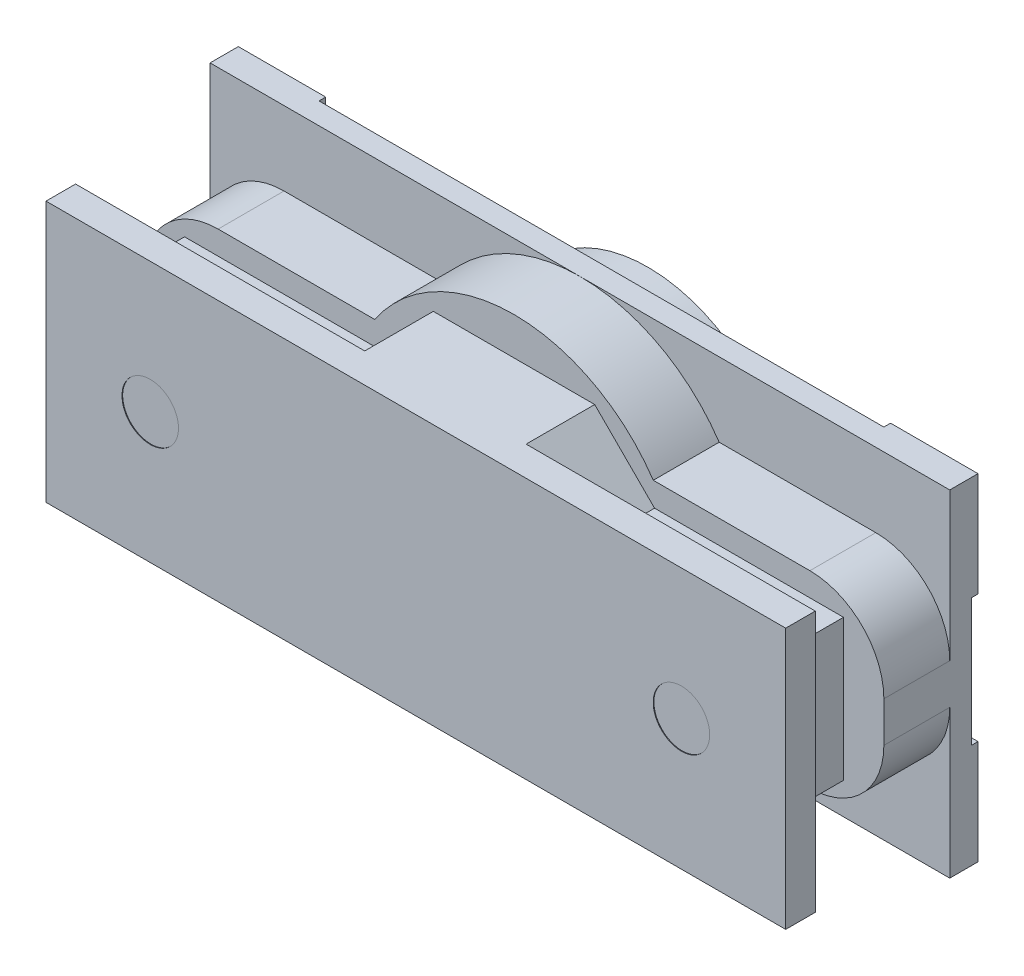
SolidWorks part; units mm, degrees
ref_plane "Płaszczyzna przednia" through (0, 0, 0) normal (0, 0, 1) x (1, 0, 0)
ref_plane "Płaszczyzna górna" through (0, 0, 0) normal (0, 1, 0) x (1, 0, 0)
ref_plane "Płaszczyzna prawa" through (0, 0, 0) normal (1, 0, 0) x (0, 0, -1)
sketch "Szkic1" plane through (0, 0, 0) normal (0, 0, 1) x (1, 0, 0)
  line L1 (-55, -25) -> (55, -25)
  line L2 (-55, -25) -> (-55, 25)
  line L3 (-55, 25) -> (55, 25)
  line L4 (55, -25) -> (55, 25)
  line L5 (-55, -25) -> (55, 25) construction
  line L6 (-55, 25) -> (55, -25) construction
  point P0 (0, 0)
  dimension "D1" = 110
  dimension "D2" = 50
extrude "Dodanie-wyciągnięcie1" add sketch "Szkic1" along normal blind 4.2
sketch "Szkic2" plane through (0, 0, 0) normal (0, 0, 1) x (1, 0, 0)
  circle A0 centre (0, 0) radius 21.15
  dimension "D1" = 42.3
extrude "Dodanie-wyciągnięcie2" add sketch "Szkic2" against normal blind 5.9
sketch "Szkic3" plane through (0, 0, 4.2) normal (0, 0, 1) x (1, 0, 0)
  line L0 (55, -25) -> (55, 25) construction
  line L1 (-55, -14) -> (55, -14)
  line L2 (-55, -14) -> (-55, 14)
  line L3 (-55, 14) -> (55, 14)
  line L4 (55, -14) -> (55, 14)
  line L5 (-55, -14) -> (55, 14) construction
  line L6 (-55, 14) -> (55, -14) construction
  circle A0 centre (0, 0) radius 25
  point P0 (0, 0)
  line M6 (55, -25) -> (55, 25)
  line M8 (-55, 25) -> (-55, -25)
  dimension "D2" = 50
  dimension "D1" = 28
extrude "Dodanie-wyciągnięcie3" add sketch "Szkic3" along normal blind 9.8 contours A0 L3 L1 M8 | L3 A0 L1 | L3 A0 | A0 L1 L3 M6 | L1 A0
fillet "Zaokrąglenie1" radius 11 4 edges at (-55, -14, 9.1) (55, -14, 9.1) (55, 14, 9.1) (-55, 14, 9.1)
sketch "Szkic4" plane through (0, 0, 14) normal (0, 0, 1) x (1, 0, 0)
  line L0 (12, 19.4) -> (20.9, 10.5)
  line L1 (-49, -10.5) -> (-20.9, -10.5)
  line L2 (-49, -10.5) -> (-49, 10.5)
  line L3 (-49, 10.5) -> (-20.9, 10.5)
  line L4 (49, -10.5) -> (49, 10.5)
  line L5 (-49, -10.5) -> (49, 10.5) construction
  line L6 (-49, 10.5) -> (49, -10.5) construction
  line L7 (-12, -19.4) -> (12, -19.4)
  line L9 (-12, 19.4) -> (12, 19.4)
  line L11 (-12, -19.4) -> (12, 19.4) construction
  line L12 (-12, 19.4) -> (12, -19.4) construction
  line L13 (-12, 19.4) -> (-20.9, 10.5)
  line L14 (-20.9, -10.5) -> (-12, -19.4)
  line L15 (20.9, -10.5) -> (12, -19.4)
  line L16 (20.9, -10.5) -> (49, -10.5)
  line L17 (20.9, 10.5) -> (49, 10.5)
  point P0 (0, 0)
  point P6 (0, 0)
  dimension "D1" = 98
  dimension "D2" = 21
  dimension "D3" = 38.8
  dimension "D4" = 24
  dimension "D5" = 45
  dimension "D6" = 45
  dimension "D7" = 45
  dimension "D8" = 45
  dimension "D9" = 19.4
  dimension "D10" = 19.4
extrude "Dodanie-wyciągnięcie4" add sketch "Szkic4" along normal blind 10.2
sketch "Szkic5" plane through (0, 0, 24.2) normal (0, 0, 1) x (1, 0, 0)
  line L0 (55, -25) -> (55, 25) construction
  line L1 (-55, -19.4) -> (55, -19.4)
  line L2 (-55, -19.4) -> (-55, 19.4)
  line L3 (-55, 19.4) -> (55, 19.4)
  line L4 (55, -19.4) -> (55, 19.4)
  line L5 (-55, -19.4) -> (55, 19.4) construction
  line L6 (-55, 19.4) -> (55, -19.4) construction
  point P0 (0, 0)
  dimension "D1" = 38.8
extrude "Dodanie-wyciągnięcie5" add sketch "Szkic5" along normal blind 4.4
sketch "Szkic6" plane through (0, 0, 28.6) normal (0, 0, 1) x (1, 0, 0)
  line L0 (0, 0) -> (39.5, 0) construction
  line L1 (0, 0) -> (-39.5, 0) construction
  circle A0 centre (-39.5, 0) radius 4.2
  circle A1 centre (39.5, 0) radius 4.2
  dimension "D3" = 8.4
  dimension "D4" = 8.4
  dimension "D1" = 39.5
  dimension "D2" = 39.5
extrude "Wytnij-wyciągnięcie1" cut sketch "Szkic6" against normal blind 0.1
sketch "Szkic7" plane through (0, 0, 0) normal (0, 0, -1) x (-1, 0, 0)
  line L0 (43, 0) -> (-41, 0)
  line L2 (55, 25) -> (42, 25)
  line L3 (-55, 25) -> (55, 25)
  line L4 (-55, 25) -> (-55, -25)
  line L5 (-55, -25) -> (55, -25)
  line L6 (55, 25) -> (55, -25)
  line L7 (-55, 25) -> (55, -25) construction
  line L8 (-55, -25) -> (55, 25) construction
  line L9 (-55, 25) -> (-42, 25)
  line L10 (-55, 25) -> (-55, 9.5)
  line L11 (-55, 9.5) -> (-42, 9.5)
  line L12 (-42, 25) -> (-42, 9.5)
  line L13 (-55, -25) -> (-42, -25)
  line L14 (-55, -25) -> (-55, -9.5)
  line L15 (-55, -9.5) -> (-42, -9.5)
  line L16 (-42, -25) -> (-42, -9.5)
  line L17 (55, -25) -> (42, -25)
  line L18 (55, -25) -> (55, -9.5)
  line L19 (55, -9.5) -> (42, -9.5)
  line L20 (42, -25) -> (42, -9.5)
  line L21 (55, 25) -> (55, 9.5)
  line L22 (55, 9.5) -> (42, 9.5)
  line L23 (42, 25) -> (42, 9.5)
  circle A0 centre (43, 0) radius 7
  circle A1 centre (43, 0) radius 9.3
  circle A2 centre (-41, 0) radius 7
  circle A3 centre (-41, 0) radius 9.3
  point P7 (0, 0)
  dimension "D3" = 14
  dimension "D4" = 18.6
  dimension "D5" = 14
  dimension "D6" = 18.6
  dimension "D1" = 84
  dimension "D2" = 41
  dimension "D7" = 13
  dimension "D8" = 15.5
extrude "Wytnij-wyciągnięcie2" cut sketch "Szkic7" against normal blind 1
